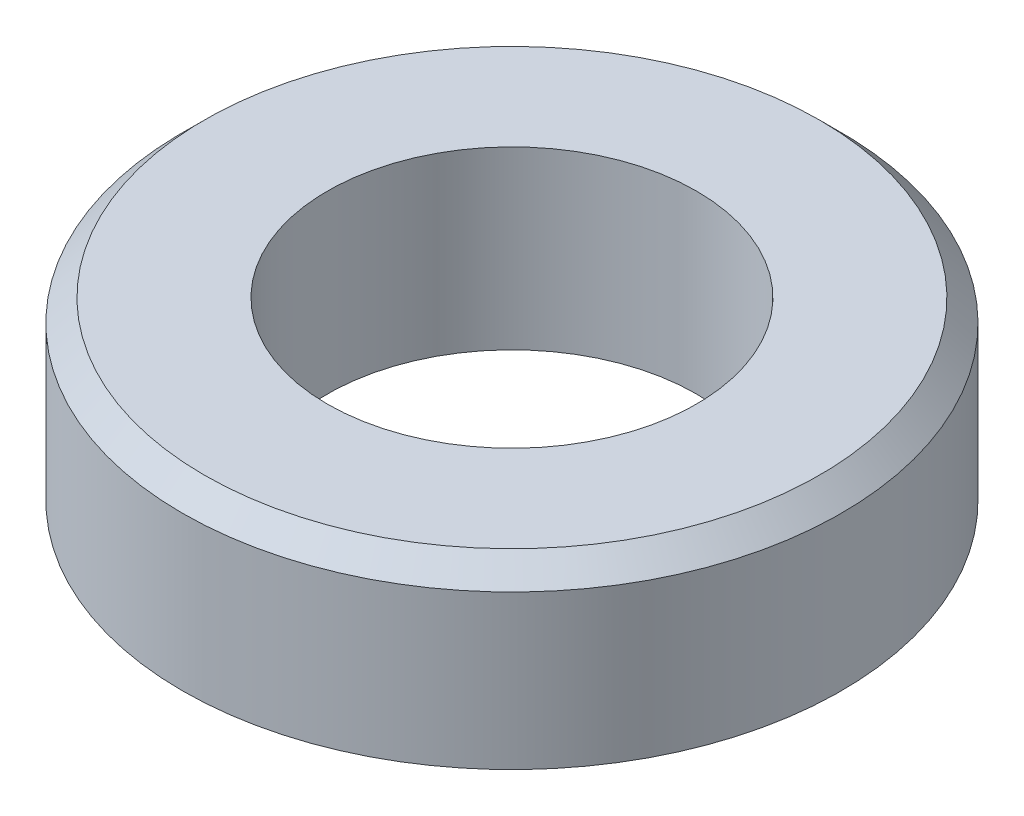
SolidWorks part; units mm, degrees
ref_plane "Front Plane" through (0, 0, 0) normal (0, 0, 1) x (1, 0, 0)
ref_plane "Top Plane" through (0, 0, 0) normal (0, 1, 0) x (1, 0, 0)
ref_plane "Right Plane" through (0, 0, 0) normal (1, 0, 0) x (0, 0, -1)
sketch "Sketch1" plane through (0, 0, 0) normal (0, 1, 0) x (1, 0, 0)
  circle A0 centre (0, 0) radius 4.2
  circle A1 centre (0, 0) radius 7.5
  dimension "D1" = 8.4
  dimension "D2" = 15
extrude "Boss-Extrude1" add sketch "Sketch1" along normal blind 4
chamfer "Chamfer1" distance 0.5 angle 45 1 edges at (0, 4, 7.5)
